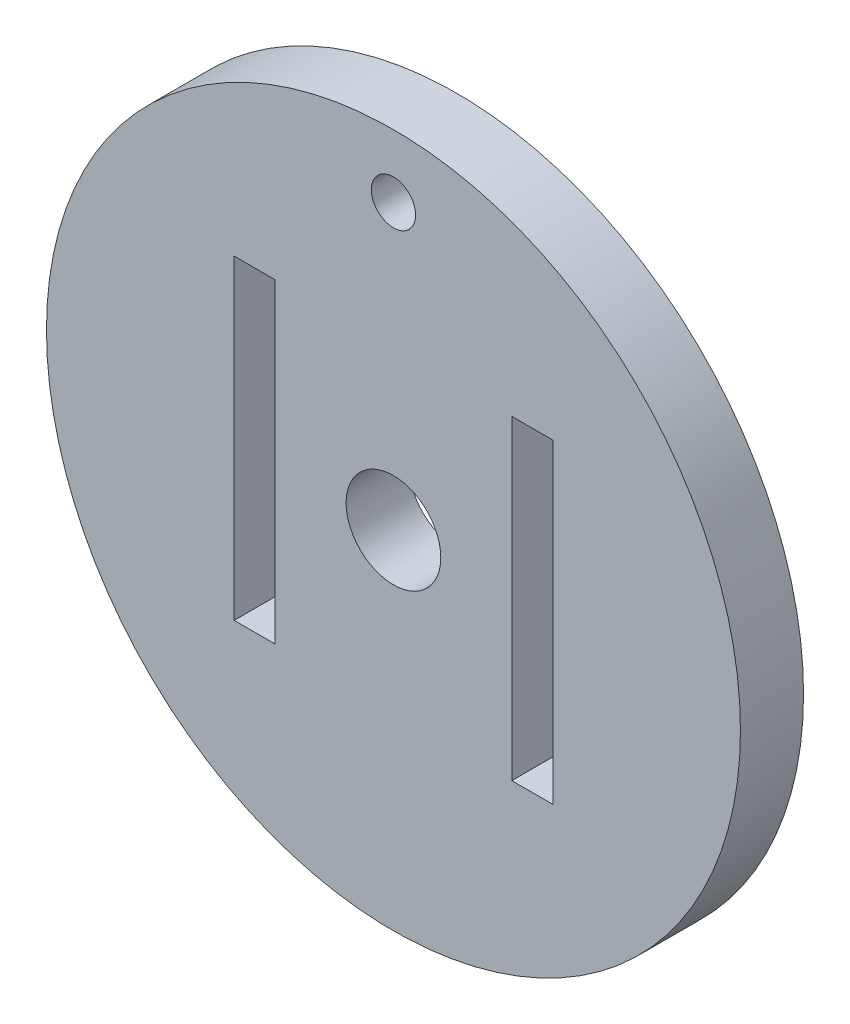
SolidWorks part; units mm, degrees
material "Acrylic (Medium-high impact)"
ref_plane "Front Plane" through (0, 0, 0) normal (0, 0, 1) x (1, 0, 0)
ref_plane "Top Plane" through (0, 0, 0) normal (0, 1, 0) x (1, 0, 0)
ref_plane "Right Plane" through (0, 0, 0) normal (1, 0, 0) x (0, 0, -1)
sketch "Sketch1" plane through (0, 0, 0) normal (0, 0, 1) x (1, 0, 0)
  line L1 (-5.05, 5) -> (-3.75, 5)
  line L2 (-5.05, 5) -> (-5.05, -5)
  line L3 (-5.05, -5) -> (-3.75, -5)
  line L4 (-3.75, 5) -> (-3.75, -5)
  line L5 (3.75, 5) -> (5.05, 5)
  line L6 (3.75, 5) -> (3.75, -5)
  line L7 (3.75, -5) -> (5.05, -5)
  line L8 (5.05, 5) -> (5.05, -5)
  circle A0 centre (0, 0) radius 11
  circle A1 centre (0, 0) radius 1.5
  circle A2 centre (0, 9) radius 0.7
  dimension "D1" = 10
  dimension "D2" = 22
  dimension "D3" = 1.4
  dimension "D8" = 3
  dimension "D4" = 9
  dimension "D5" = 3.75
  dimension "D6" = 3.75
  dimension "D7" = 1.3
  dimension "D9" = 5
  dimension "D10" = 5
extrude "Boss-Extrude1" add sketch "Sketch1" along normal blind 2
